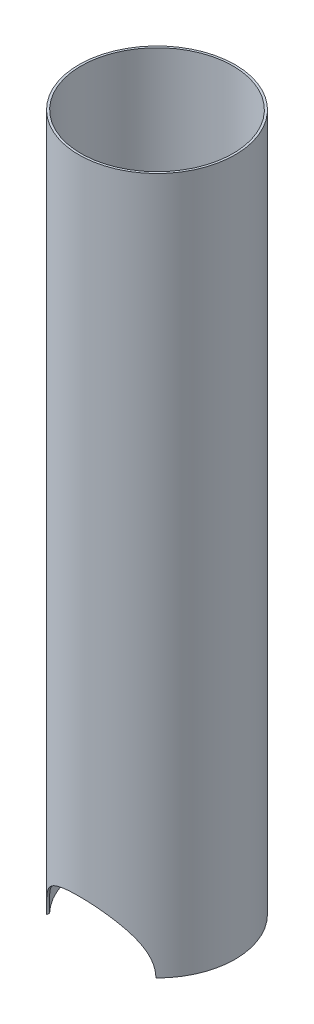
SolidWorks part; units mm, degrees
ref_plane "Front" through (0, 0, 0) normal (0, 0, 1) x (1, 0, 0)
ref_plane "Top" through (0, 0, 0) normal (0, 1, 0) x (1, 0, 0)
ref_plane "Right" through (0, 0, 0) normal (1, 0, 0) x (0, 0, -1)
ref_plane "Plane1" through (0, -110, 0) normal (0, 1, 0) x (1, 0, 0)
sketch "Sketch1" plane through (0, 0, 0) normal (0, 1, 0) x (1, 0, 0)
  circle A0 centre (0, 0) radius 57.15
  circle A1 centre (0, 0) radius 55.5625
  dimension "D1" = 114.3
  dimension "D2" = 1.5875
extrude "OEM" add sketch "Sketch1" along normal blind 457.2 and the other way blind 152.4
sketch "Sketch5" plane through (0, 0, 0) normal (0, 0, 1) x (1, 0, 0)
  line L0 (-57.15, -152.4) -> (57.15, -152.4) construction
  line L1 (-40, -152.4) -> (40, -152.4) construction
  arc A0 (40, -152.4) -> (-40, -152.4) centre (0, -152.4) ccw
  dimension "D1" = 40
extrude "eNSR baseplate cutout" cut sketch "Sketch5" against normal through all both and the other way through all
sketch "Sketch6" plane through (0, 0, 0) normal (0, 0, 1) x (1, 0, 0)
  line L0 (57.15, -152.4) -> (57.15, 457.2) construction
  line L1 (-57.15, 457.2) -> (57.15, 457.2)
  line L2 (-57.15, 457.2) -> (-57.15, 357.2)
  line L3 (-57.15, 357.2) -> (57.15, 357.2)
  line L4 (57.15, 457.2) -> (57.15, 357.2)
  dimension "D1" = 100
extrude "too long" cut sketch "Sketch6" against normal through all both and the other way through all
sketch "Sketch7" plane through (0, -110, 0) normal (0, 1, 0) x (1, 0, 0)
  circle A1 centre (52.3875, 0) radius 3.175
  circle A2 centre (52.3875, 0) radius 4.7625
  dimension "D1" = 6.35
  dimension "D2" = 1.5875
extrude "conduit" add sketch "Sketch7" along normal blind 300 and the other way blind 10
sketch "Sketch3" plane through (0, -110, 0) normal (0, 1, 0) x (1, 0, 0)
  circle A0 centre (0, 0) radius 57.15
  circle A1 centre (52.3875, 0) radius 3.175
  dimension "D1" = 114.3
extrude "floor" add sketch "Sketch3" along normal blind 1.5875
